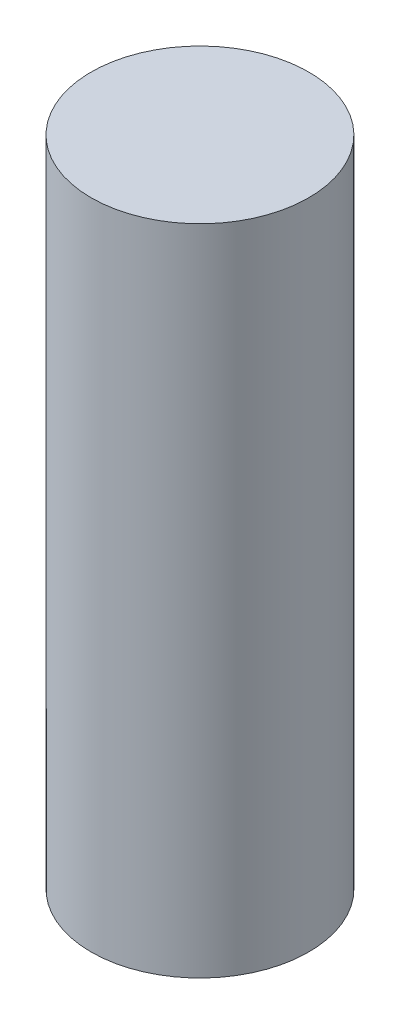
SolidWorks part; units mm, degrees
ref_plane "Ebene vorne" through (0, 0, 0) normal (0, 0, 1) x (1, 0, 0)
ref_plane "Ebene oben" through (0, 0, 0) normal (0, 1, 0) x (1, 0, 0)
ref_plane "Ebene rechts" through (0, 0, 0) normal (1, 0, 0) x (0, 0, -1)
sketch "Skizze1" plane through (0, 0, 0) normal (0, 1, 0) x (1, 0, 0)
  circle A0 centre (0, 0) radius 1
extrude "Aufsatz-Linear austragen1" add sketch "Skizze1" along normal blind 6
